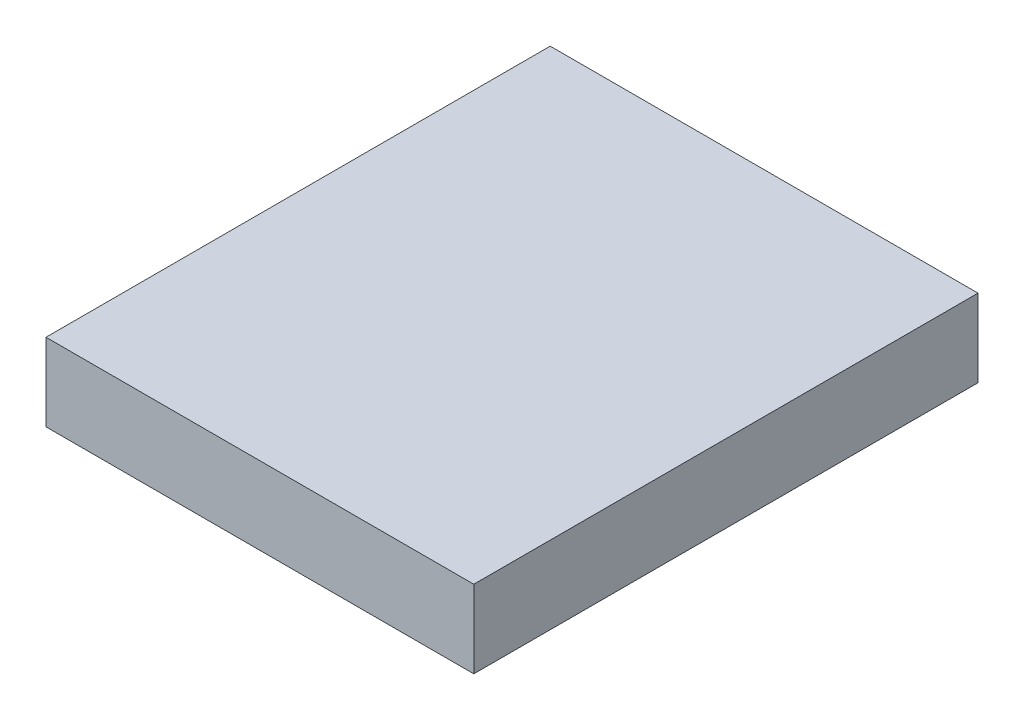
SolidWorks part; units mm, degrees
ref_plane "Front Plane" through (0, 0, 0) normal (0, 0, 1) x (1, 0, 0)
ref_plane "Top Plane" through (0, 0, 0) normal (0, 1, 0) x (1, 0, 0)
ref_plane "Right Plane" through (0, 0, 0) normal (1, 0, 0) x (0, 0, -1)
sketch "Sketch1" plane through (0, 0, 0) normal (0, 1, 0) x (1, 0, 0)
  line L1 (0, 0) -> (70, 0)
  line L2 (0, 0) -> (0, 82.5)
  line L3 (0, 82.5) -> (70, 82.5)
  line L4 (70, 0) -> (70, 82.5)
  dimension "D1" = 82.5
  dimension "D2" = 70
extrude "Boss-Extrude1" add sketch "Sketch1" along normal blind 12.7
